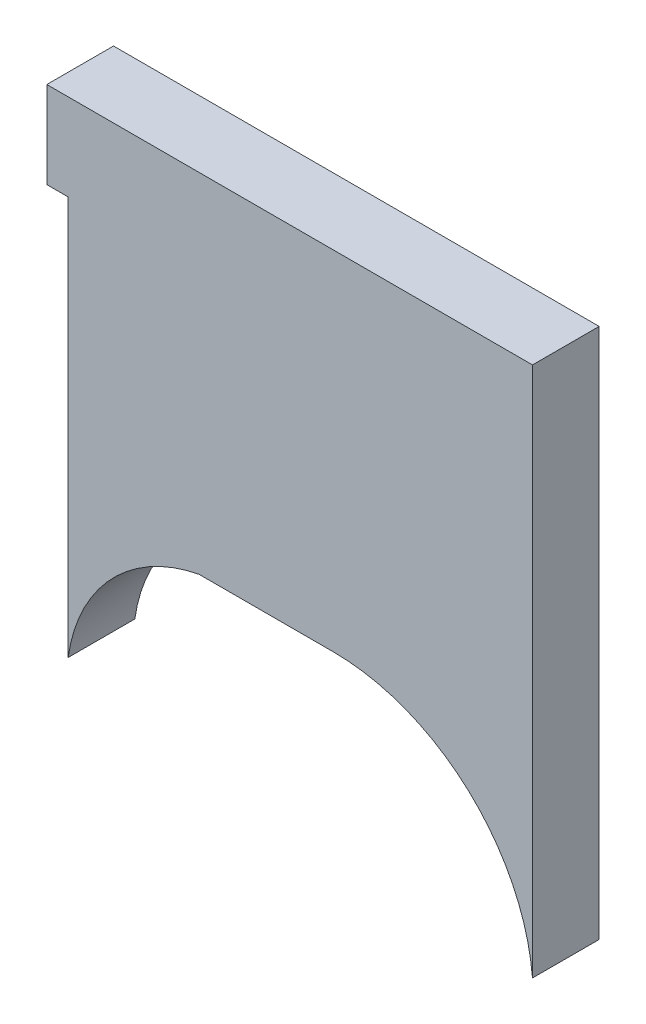
SolidWorks part; units mm, degrees
ref_plane "Front Plane" through (0, 0, 0) normal (0, 0, 1) x (1, 0, 0)
ref_plane "Top Plane" through (0, 0, 0) normal (0, 1, 0) x (1, 0, 0)
ref_plane "Right Plane" through (0, 0, 0) normal (1, 0, 0) x (0, 0, -1)
sketch "Sketch3" plane through (0, 0, 0) normal (0, 0, 1) x (1, 0, 0)
  line L14 (30.2935, -9.1627) -> (26.8246, -9.1627)
  line L24 (39.7832, -6.6227) -> (39.7832, 7.4068)
  line L25 (39.7832, -6.6227) -> (39.7832, -9.1627)
  line L27 (23.9103, -9.1627) -> (26.8246, -9.1627)
  line L29 (17.6796, 3.2793) -> (16.6646, 3.2793)
  line L30 (16.6646, 3.2793) -> (16.6646, 7.4068)
  line L31 (16.6646, 7.4068) -> (38.516, 7.4068)
  line L33 (17.6796, -15.708) -> (17.6796, 3.2793)
  line L35 (39.7832, -17.868) -> (39.7832, -9.1627)
  line L36 (39.7832, 7.4068) -> (38.516, 7.4068)
  arc A4 (30.2935, -9.1627) -> (39.7832, -17.868) centre (30.2935, -18.6877) cw
  arc A6 (17.6796, -15.708) -> (23.9103, -9.1627) centre (25.3674, -16.788) cw
  dimension "D2" = 9.525
  dimension "D9" = 4.1275
extrude "Boss-Extrude3" add sketch "Sketch3" along normal blind 3.175
